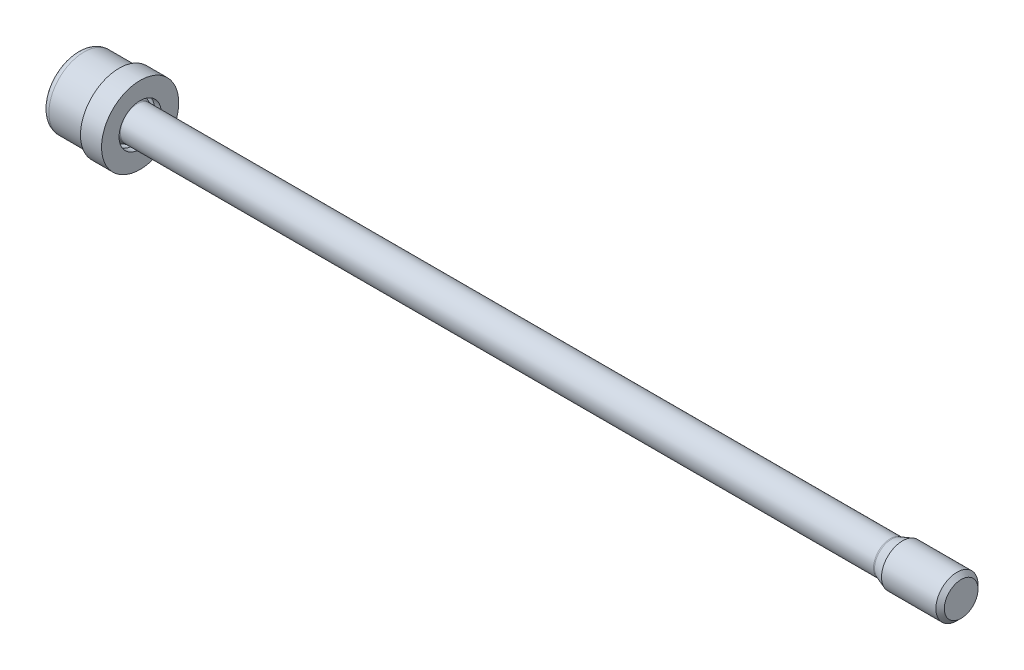
SolidWorks part; units mm, degrees
material "Ti-6Al-2Sn-2Zr-2Mo-2Cr-0.25Si (SS)"
ref_plane "Ebene XY" through (0, 0, 0) normal (0, 0, 1) x (1, 0, 0)
ref_plane "Ebene XZ" through (0, 0, 0) normal (0, 1, 0) x (1, 0, 0)
ref_plane "Ebene YZ" through (0, 0, 0) normal (1, 0, 0) x (0, 0, -1)
sketch "Skizze1" plane through (0, 0, 0) normal (0, 0, 1) x (1, 0, 0)
  line L0 (0, 0) -> (-40.2429, 0) construction
  line L1 (55, 0) -> (-55, 0) construction
  line L2 (0, 5) -> (6, 5)
  line L3 (0, -55) -> (0, 55) construction
  line L4 (6, 5) -> (6, 3.3099)
  line L5 (6, 3.3099) -> (8.5, 2.4)
  line L6 (8.5, 2.4) -> (116, 2.4)
  line L7 (116, 2.4) -> (117.6485, 3)
  line L8 (117.6485, 3) -> (125.4, 3)
  line L9 (125.4, 3) -> (126, 2.4)
  line L10 (126, 2.4) -> (126, 0)
  line L11 (126, 0) -> (4.7321, 0)
  line L12 (4.7321, 0) -> (3, 3)
  line L13 (3, 3) -> (0, 3)
  line L14 (0, 3) -> (0, 5)
  dimension "D1" = 2.5
  dimension "D2" = 20
  dimension "D3" = 120
  dimension "D4" = 20
  dimension "D5" = 4.8
  dimension "D6" = 6
  dimension "D7" = 110
  dimension "D8" = 45
  dimension "D9" = 6
  dimension "D10" = 10
  dimension "D11" = 6
  dimension "D12" = 60
  dimension "D13" = 3
revolve "Rotation1" add sketch "Skizze1" angle 360 about L0
cosmetic thread "Gewindedarstellung1" parameters "D2"=4.891
sketch "Skizze2" plane through (0, 0, 0) normal (-1, 0, 0) x (0, 0, 1)
  line L1 (-2.8868, 0) -> (-1.4434, -2.5)
  line L2 (-1.4434, -2.5) -> (1.4434, -2.5)
  line L3 (1.4434, -2.5) -> (2.8868, 0)
  line L4 (2.8868, 0) -> (1.4434, 2.5)
  line L5 (1.4434, 2.5) -> (-1.4434, 2.5)
  line L6 (-1.4434, 2.5) -> (-2.8868, 0)
  circle A0 centre (0, 0) radius 2.5 construction
  circle A1 centre (0, 0) radius 3 construction
  circle A2 centre (0, 0) radius 3
  dimension "D1" = 5
extrude "Aufsatz-Linear austragen1" add sketch "Skizze2" against normal up to surface (3 mm away)
fillet "Verrundung1" radius 1 1 edges at (0, 0, -5)
fillet "Verrundung2" radius 0.5 3 edges at (116, 0, -2.4) (8.5, 0, -2.4) (6, 0, -3.3099)
sketch "Skizze3" plane through (0, 0, 0) normal (0, 0, 1) x (1, 0, 0)
  line L0 (6, 5.5) -> (9, 5.5)
  line L1 (9, 5.5) -> (9, 3)
  line L2 (9, 3) -> (8.0606, 3)
  line L3 (6, -5) -> (6, 5) construction
  line L4 (6, 3.75) -> (6, 5.5)
  line L5 (8.0606, 3) -> (6, 3.75)
  line L6 (0, 0) -> (9.2776, 0) construction
  line L7 (55, 0) -> (-55, 0) construction
  dimension "D1" = 6
  dimension "D2" = 7.5
  dimension "D3" = 20
  dimension "D4" = 3
  dimension "D5" = 11
revolve "Rotation2" add sketch "Skizze3" angle 360 about L6
move or copy body "Körper-Verschieben/Kopieren1" [suppressed] bodies to move or copy 103 copy no translate (0, 0, -16)
